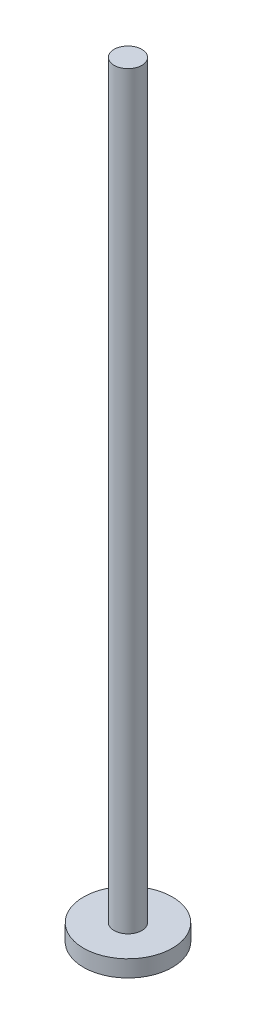
SolidWorks part; units mm, degrees
material "6061-T6 (SS)"
ref_plane "前视基准面" through (0, 0, 0) normal (0, 0, 1) x (1, 0, 0)
ref_plane "上视基准面" through (0, 0, 0) normal (0, 1, 0) x (1, 0, 0)
ref_plane "右视基准面" through (0, 0, 0) normal (1, 0, 0) x (0, 0, -1)
sketch "草图1" plane through (0, 0, 0) normal (0, 1, 0) x (1, 0, 0)
  circle A0 centre (0, 0) radius 8
  dimension "D1" = 16
extrude "凸台-拉伸1" add sketch "草图1" along normal blind 3
sketch "草图2" plane through (0, 3, 0) normal (0, 1, 0) x (1, 0, 0)
  circle A0 centre (0, 0) radius 2.5
  dimension "D1" = 5
extrude "凸台-拉伸2" add sketch "草图2" along normal blind 135
equation "\"行程L\"= 50"
equation "\"D1@凸台-拉伸2\"=\"行程L\"+50"
